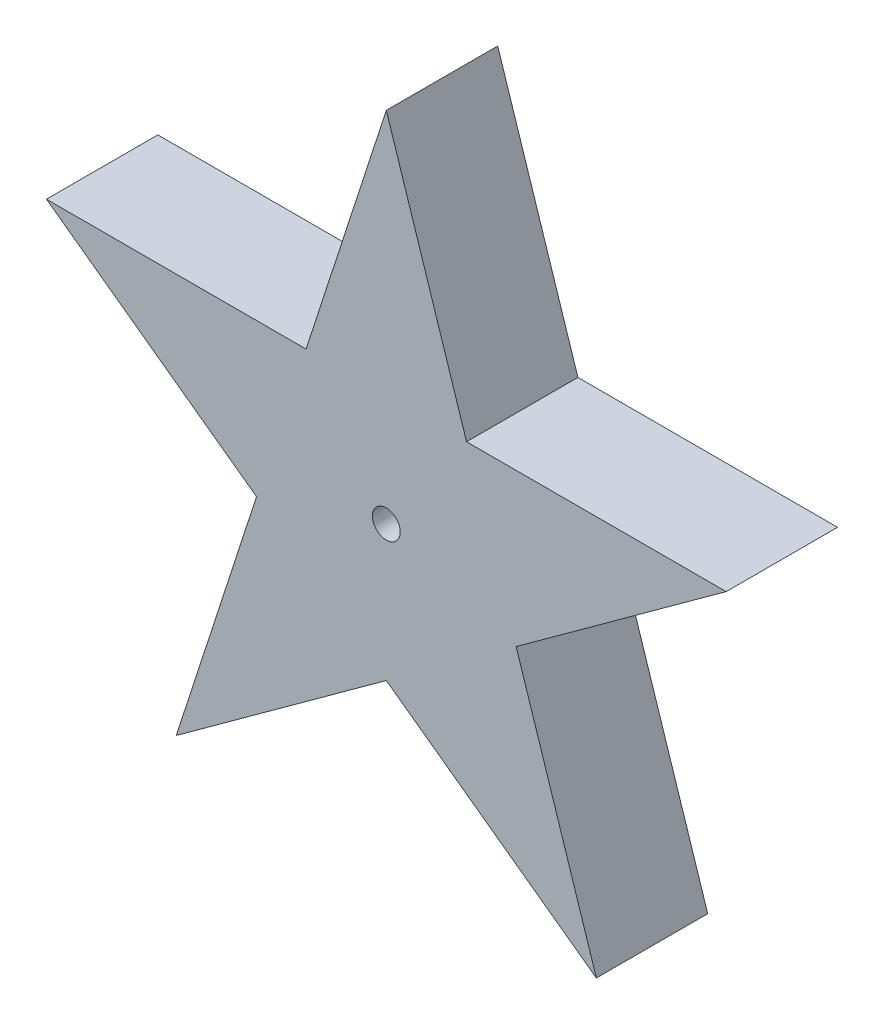
SolidWorks part; units mm, degrees
ref_plane "Plan de face" through (0, 0, 0) normal (0, 0, 1) x (1, 0, 0)
ref_plane "Plan de dessus" through (0, 0, 0) normal (0, 1, 0) x (1, 0, 0)
ref_plane "Plan de droite" through (0, 0, 0) normal (1, 0, 0) x (0, 0, -1)
sketch "Esquisse1" plane through (0, 0, 0) normal (0, 0, 1) x (1, 0, 0)
  line L0 (-0.7204, 1) -> (0.7204, 1)
  line L1 (0.7204, 1) -> (1.1657, -0.3703)
  line L2 (1.1657, -0.3703) -> (0, -1.2172)
  line L3 (0, -1.2172) -> (-1.1657, -0.3703)
  line L4 (-1.1657, -0.3703) -> (-0.7204, 1)
  line L5 (-0.7204, 1) -> (0, 3.2172)
  line L6 (0, 3.2172) -> (0.7204, 1)
  line L7 (-1.1657, -0.3703) -> (-1.8861, -2.5875)
  line L8 (-1.8861, -2.5875) -> (0, -1.2172)
  line L9 (-0.7204, 1) -> (-3.0518, 1)
  line L10 (-3.0518, 1) -> (-1.1657, -0.3703)
  line L11 (0, -1.2172) -> (1.8861, -2.5875)
  line L12 (1.8861, -2.5875) -> (1.1657, -0.3703)
  line L13 (0.7204, 1) -> (3.0518, 1)
  line L14 (3.0518, 1) -> (1.1657, -0.3703)
  dimension "D1" = 108
  dimension "D2" = 108
  dimension "D3" = 3.2172
  dimension "D4" = 1.1657
  dimension "D5" = 1.1657
sketch "Esquisse3" plane through (0, 0, 0) normal (0, 0, 1) x (1, 0, 0)
  line L0 (0, 3.2172) -> (0.7204, 1)
  line L1 (0.7204, 1) -> (3.0518, 1)
  line L2 (3.0518, 1) -> (1.1657, -0.3703)
  line L3 (1.1657, -0.3703) -> (1.8861, -2.5875)
  line L4 (1.8861, -2.5875) -> (0, -1.2172)
  line L5 (0, -1.2172) -> (-1.8861, -2.5875)
  line L6 (-1.8861, -2.5875) -> (-1.1657, -0.3703)
  line L7 (-1.1657, -0.3703) -> (-3.0518, 1)
  line L8 (-3.0518, 1) -> (-0.7204, 1)
  line L9 (-0.7204, 1) -> (0, 3.2172)
extrude "Boss.-Extru.1" add sketch "Esquisse3" along normal blind 1
sketch "Esquisse4" plane through (0, 0, 0) normal (0, 0, -1) x (-1, 0, 0)
  circle A0 centre (0, 0) radius 0.125
  dimension "D1" = 0.25
extrude "Enlèv. mat.-Extru.1" cut sketch "Esquisse4" against normal through all
equation "\"D2@Esquisse1\" = \"D1@Esquisse1\""
equation "\"D3@Esquisse1\" = \"D1@Esquisse1\""
equation "\"D4@Esquisse1\" = \"D1@Esquisse1\""
equation "\"D5@Esquisse1\" = \"D4@Esquisse1\""
